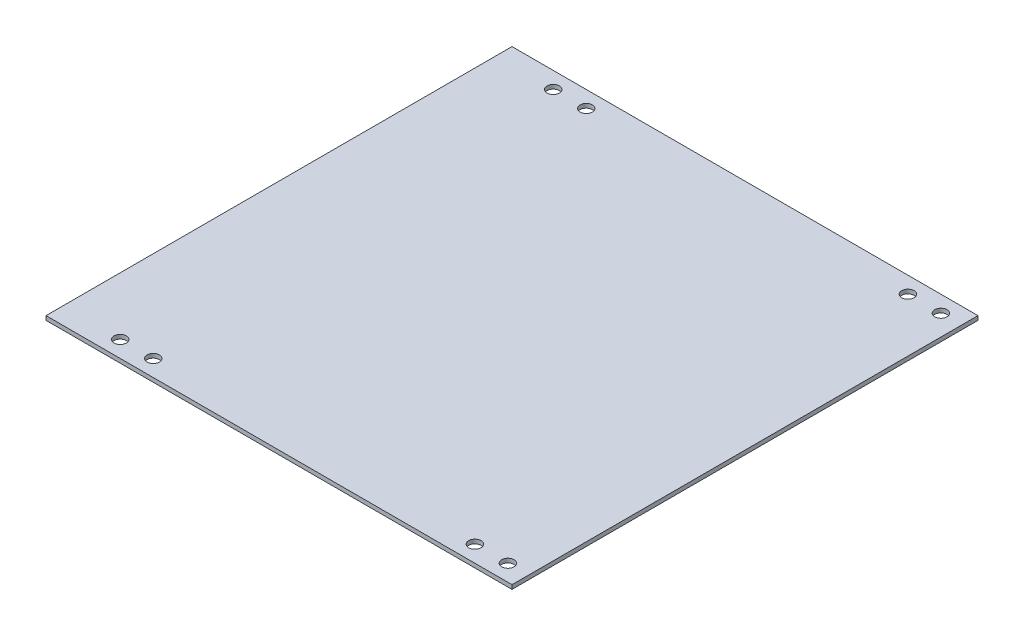
SolidWorks part; units mm, degrees
material "PC High Viscosity"
ref_plane "Front Plane" through (0, 0, 0) normal (0, 0, 1) x (1, 0, 0)
ref_plane "Top Plane" through (0, 0, 0) normal (0, 1, 0) x (1, 0, 0)
ref_plane "Right Plane" through (0, 0, 0) normal (1, 0, 0) x (0, 0, -1)
sketch "Sketch1" plane through (0, 0, 0) normal (0, 1, 0) x (1, 0, 0)
  line L0 (0, 0) -> (358.775, 0)
  line L1 (0, 0) -> (0, 358.775)
  line L2 (358.775, 0) -> (358.775, 358.775)
  line L3 (0, 358.775) -> (358.775, 358.775)
  dimension "D1" = 358.775
  dimension "D2" = 358.775
extrude "Boss-Extrude1" add sketch "Sketch1" along normal blind 3.175
ref_plane "Plane1" through (0, 0, -179.3875) normal (0, 0, 1) x (1, 0, 0)
sketch "Sketch2" plane through (0, 3.175, 0) normal (0, 1, 0) x (1, 0, 0)
  line L0 (358.775, 0) -> (358.775, 358.775) construction
  line L1 (0, 0) -> (358.775, 0) construction
  circle A0 centre (44.45, 12.7) radius 4.7625
  circle A1 centre (69.85, 12.7) radius 4.7625
  circle A2 centre (317.5, 12.7) radius 4.7625
  circle A3 centre (342.9, 12.7) radius 4.7625
  dimension "D1" = 9.525
  dimension "D2" = 25.4
  dimension "D3" = 25.4
  dimension "D4" = 15.875
  dimension "D5" = 288.925
  dimension "D6" = 12.7
extrude "Cut-Extrude1" cut sketch "Sketch2" against normal through all
mirror "Mirror1" about plane through (0, 0, -179.3875) normal (0, 0, 1) of "Cut-Extrude1"
